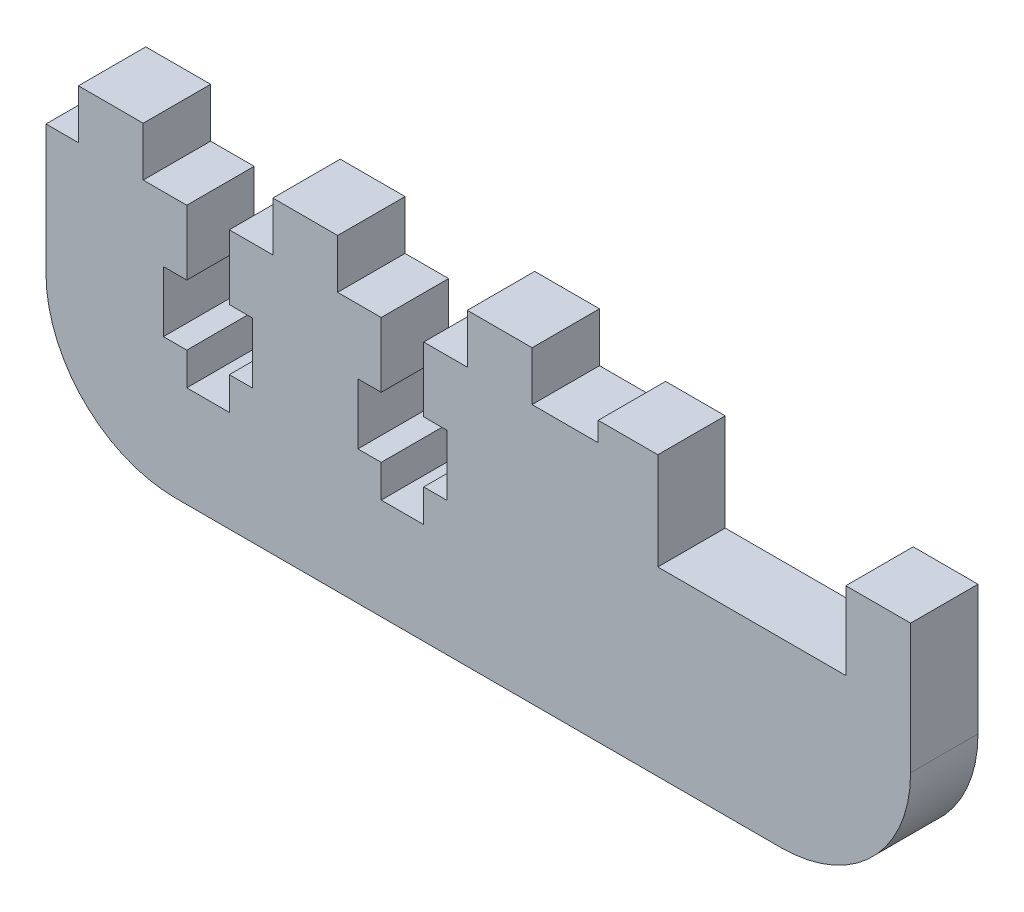
SolidWorks part; units mm, degrees
material "Acrylic (Blue)"
ref_plane "Front Plane" through (0, 0, 0) normal (0, 0, 1) x (1, 0, 0)
ref_plane "Top Plane" through (0, 0, 0) normal (0, 1, 0) x (1, 0, 0)
ref_plane "Right Plane" through (0, 0, 0) normal (1, 0, 0) x (0, 0, -1)
sketch "Sketch1" plane through (0, 0, 0) normal (0, 0, 1) x (1, 0, 0)
  line L1 (12.7, 0) -> (-12.7, 0) construction
  line L2 (12.7, 0) -> (12.7, 3.175) construction
  line L3 (12.7, 3.175) -> (-12.7, 3.175) construction
  line L4 (-12.7, 0) -> (-12.7, 3.175) construction
  line L5 (-12.827, 3.175) -> (-89.027, 3.175) construction
  line L6 (-12.827, 3.175) -> (-12.827, -1.905) construction
  line L7 (-12.827, -1.905) -> (-89.027, -1.905) construction
  line L8 (-89.027, 3.175) -> (-89.027, -1.905) construction
  line L9 (12.827, 3.175) -> (89.027, 3.175) construction
  line L10 (12.827, 3.175) -> (12.827, -1.905) construction
  line L11 (12.827, -1.905) -> (89.027, -1.905) construction
  line L12 (89.027, 3.175) -> (89.027, -1.905) construction
  line L13 (12.7, 3.175) -> (12.827, 3.175) construction
  line L14 (-12.7, 3.175) -> (-12.827, 3.175) construction
  line L16 (-6.858, 0) -> (-6.858, -9.525)
  line L17 (-6.858, -9.525) -> (11.557, -9.525)
  line L18 (17.907, -1.905) -> (11.557, -1.905)
  line L19 (-6.858, 0) -> (-12.7, 0)
  line L20 (-12.7, 0) -> (-12.7, -1.905)
  line L21 (-12.7, -1.905) -> (-66.802, -1.905)
  line L22 (-66.802, -1.905) -> (-66.802, -27.305)
  line L23 (-66.802, -27.305) -> (17.907, -27.305)
  line L24 (17.907, -1.905) -> (17.907, -27.305)
  line L26 (11.557, -1.905) -> (11.557, -9.525)
  line B0 (-53.0098, -1.905) -> (-53.0098, -8.255) construction
  line B1 (-53.0098, -8.255) -> (-55.2958, -8.255) construction
  line B2 (-55.2958, -8.255) -> (-55.2958, -14.1986) construction
  line B3 (-55.2958, -14.1986) -> (-53.0098, -14.1986) construction
  line B4 (-53.0098, -14.1986) -> (-53.0098, -17.399) construction
  line B5 (-53.0098, -17.399) -> (-48.8442, -17.399) construction
  line B6 (-48.8442, -17.399) -> (-48.8442, -14.1986) construction
  line B7 (-48.8442, -14.1986) -> (-46.5582, -14.1986) construction
  line B8 (-46.5582, -14.1986) -> (-46.5582, -8.255) construction
  line B9 (-46.5582, -8.255) -> (-48.8442, -8.255) construction
  line B10 (-48.8442, -8.255) -> (-48.8442, -1.905) construction
  line B11 (-44.577, -1.905) -> (-44.577, 2.921) construction
  line B12 (-44.577, 2.921) -> (-38.227, 2.921) construction
  line B13 (-38.227, 2.921) -> (-38.227, -1.905) construction
  line B14 (-57.277, -1.905) -> (-57.277, 2.921) construction
  line B15 (-57.277, 2.921) -> (-63.627, 2.921) construction
  line B16 (-63.627, 2.921) -> (-63.627, -1.905) construction
  line B17 (-19.177, 2.921) -> (-19.177, -1.905) construction
  line B18 (-33.9598, -1.905) -> (-33.9598, -8.255) construction
  line B19 (-33.9598, -8.255) -> (-36.2458, -8.255) construction
  line B20 (-36.2458, -8.255) -> (-36.2458, -14.1986) construction
  line B21 (-36.2458, -14.1986) -> (-33.9598, -14.1986) construction
  line B22 (-33.9598, -14.1986) -> (-33.9598, -17.399) construction
  line B23 (-33.9598, -17.399) -> (-29.7942, -17.399) construction
  line B24 (-29.7942, -17.399) -> (-29.7942, -14.1986) construction
  line B25 (-29.7942, -14.1986) -> (-27.5082, -14.1986) construction
  line B26 (-27.5082, -14.1986) -> (-27.5082, -8.255) construction
  line B27 (-27.5082, -8.255) -> (-29.7942, -8.255) construction
  line B28 (-29.7942, -8.255) -> (-29.7942, -1.905) construction
  line B29 (-25.527, -1.905) -> (-25.527, 2.921) construction
  line B30 (-25.527, 2.921) -> (-19.177, 2.921) construction
  line B31 (-38.227, 2.921) -> (-44.577, 2.921) construction
  dimension "D1" = 3.175
  dimension "D2" = 25.4
  dimension "D3" = 25.654
  dimension "D4" = 5.08
  dimension "D5" = 76.2
  dimension "D6" = 18.415
  dimension "D7" = 9.525
  dimension "D8" = 6.35
  dimension "D9" = 25.4
  dimension "D10" = 6.35
  dimension "D11" = 5.842
  dimension "D12" = 3.175
sketch_block_instance "NUT_HOLE_2X-1"
sketch_block "NUT_HOLE_2X" parameters "D1"=6.35, "D2"=4.1656, "D3"=25.4, "D4"=4.826, "D5"=8.7376, "D6"=5.9436, "D7"=6.35, "D8"=20.32, "D9"=2
extrude "Boss-Extrude1" add sketch "Sketch1" along normal blind 6.604
sketch "Sketch2" plane through (0, 0, 6.604) normal (0, 0, 1) x (1, 0, 0)
  line L0 (-53.0098, -1.905) -> (-53.0098, -8.255) construction
  line L1 (-53.0098, -8.255) -> (-55.2958, -8.255) construction
  line L2 (-55.2958, -8.255) -> (-55.2958, -14.1986) construction
  line L3 (-55.2958, -14.1986) -> (-53.0098, -14.1986) construction
  line L4 (-53.0098, -14.1986) -> (-53.0098, -17.399) construction
  line L5 (-53.0098, -17.399) -> (-48.8442, -17.399) construction
  line L6 (-48.8442, -17.399) -> (-48.8442, -14.1986) construction
  line L7 (-48.8442, -14.1986) -> (-46.5582, -14.1986) construction
  line L8 (-46.5582, -14.1986) -> (-46.5582, -8.255) construction
  line L9 (-46.5582, -8.255) -> (-48.8442, -8.255) construction
  line L10 (-48.8442, -8.255) -> (-48.8442, -1.905) construction
  line L11 (-33.9598, -1.905) -> (-33.9598, -8.255) construction
  line L12 (-33.9598, -8.255) -> (-36.2458, -8.255) construction
  line L13 (-36.2458, -8.255) -> (-36.2458, -14.1986) construction
  line L14 (-36.2458, -14.1986) -> (-33.9598, -14.1986) construction
  line L15 (-33.9598, -14.1986) -> (-33.9598, -17.399) construction
  line L16 (-33.9598, -17.399) -> (-29.7942, -17.399) construction
  line L17 (-29.7942, -17.399) -> (-29.7942, -14.1986) construction
  line L18 (-29.7942, -14.1986) -> (-27.5082, -14.1986) construction
  line L19 (-27.5082, -14.1986) -> (-27.5082, -8.255) construction
  line L20 (-27.5082, -8.255) -> (-29.7942, -8.255) construction
  line L21 (-29.7942, -8.255) -> (-29.7942, -1.905) construction
  line L22 (-53.0098, -1.905) -> (-53.0098, -8.255)
  line L23 (-53.0098, -8.255) -> (-55.2958, -8.255)
  line L24 (-55.2958, -8.255) -> (-55.2958, -14.1986)
  line L25 (-55.2958, -14.1986) -> (-53.0098, -14.1986)
  line L26 (-53.0098, -14.1986) -> (-53.0098, -17.399)
  line L27 (-53.0098, -17.399) -> (-48.8442, -17.399)
  line L28 (-48.8442, -17.399) -> (-48.8442, -14.1986)
  line L29 (-48.8442, -14.1986) -> (-46.5582, -14.1986)
  line L30 (-46.5582, -14.1986) -> (-46.5582, -8.255)
  line L31 (-46.5582, -8.255) -> (-48.8442, -8.255)
  line L32 (-48.8442, -8.255) -> (-48.8442, -1.905)
  line L33 (-33.9598, -1.905) -> (-33.9598, -8.255)
  line L34 (-33.9598, -8.255) -> (-36.2458, -8.255)
  line L35 (-36.2458, -8.255) -> (-36.2458, -14.1986)
  line L36 (-36.2458, -14.1986) -> (-33.9598, -14.1986)
  line L37 (-33.9598, -14.1986) -> (-33.9598, -17.399)
  line L38 (-33.9598, -17.399) -> (-29.7942, -17.399)
  line L39 (-29.7942, -17.399) -> (-29.7942, -14.1986)
  line L40 (-29.7942, -14.1986) -> (-27.5082, -14.1986)
  line L41 (-27.5082, -14.1986) -> (-27.5082, -8.255)
  line L42 (-27.5082, -8.255) -> (-29.7942, -8.255)
  line L43 (-29.7942, -8.255) -> (-29.7942, -1.905)
  line L44 (-53.0098, -1.905) -> (-48.8442, -1.905)
  line L45 (-33.9598, -1.905) -> (-29.7942, -1.905)
extrude "Cut-Extrude1" cut sketch "Sketch2" against normal through all
sketch "Sketch3" plane through (0, 0, 6.604) normal (0, 0, 1) x (1, 0, 0)
  line L0 (-57.277, 2.921) -> (-63.627, 2.921) construction
  line L1 (-57.277, 2.921) -> (-63.627, 2.921)
  line L2 (-44.577, 2.921) -> (-38.227, 2.921) construction
  line L3 (-44.577, 2.921) -> (-38.227, 2.921)
  line L4 (-25.527, 2.921) -> (-19.177, 2.921) construction
  line L5 (-25.527, 2.921) -> (-19.177, 2.921)
  line L6 (-63.627, 2.921) -> (-63.627, -1.905) construction
  line L7 (-57.277, -1.905) -> (-57.277, 2.921) construction
  line L8 (-44.577, -1.905) -> (-44.577, 2.921) construction
  line L9 (-38.227, 2.921) -> (-38.227, -1.905) construction
  line L10 (-25.527, -1.905) -> (-25.527, 2.921) construction
  line L11 (-19.177, 2.921) -> (-19.177, -1.905) construction
  line L12 (-63.627, 2.921) -> (-63.627, -1.905)
  line L13 (-57.277, -1.905) -> (-57.277, 2.921)
  line L14 (-44.577, -1.905) -> (-44.577, 2.921)
  line L15 (-38.227, 2.921) -> (-38.227, -1.905)
  line L16 (-25.527, -1.905) -> (-25.527, 2.921)
  line L17 (-19.177, 2.921) -> (-19.177, -1.905)
  line L18 (-63.627, -1.905) -> (-57.277, -1.905)
  line L19 (-44.577, -1.905) -> (-38.227, -1.905)
  line L20 (-25.527, -1.905) -> (-19.177, -1.905)
extrude "Boss-Extrude2" add sketch "Sketch3" against normal up to surface (6.604 mm away) up to face at (-32.5718, -9.9448, 0)
fillet "Fillet1" radius 12.7 2 edges at (-66.802, -27.305, 3.302) (17.907, -27.305, 3.302)
other "Move Face1" [suppressed] parameters "D1"=0.0508
